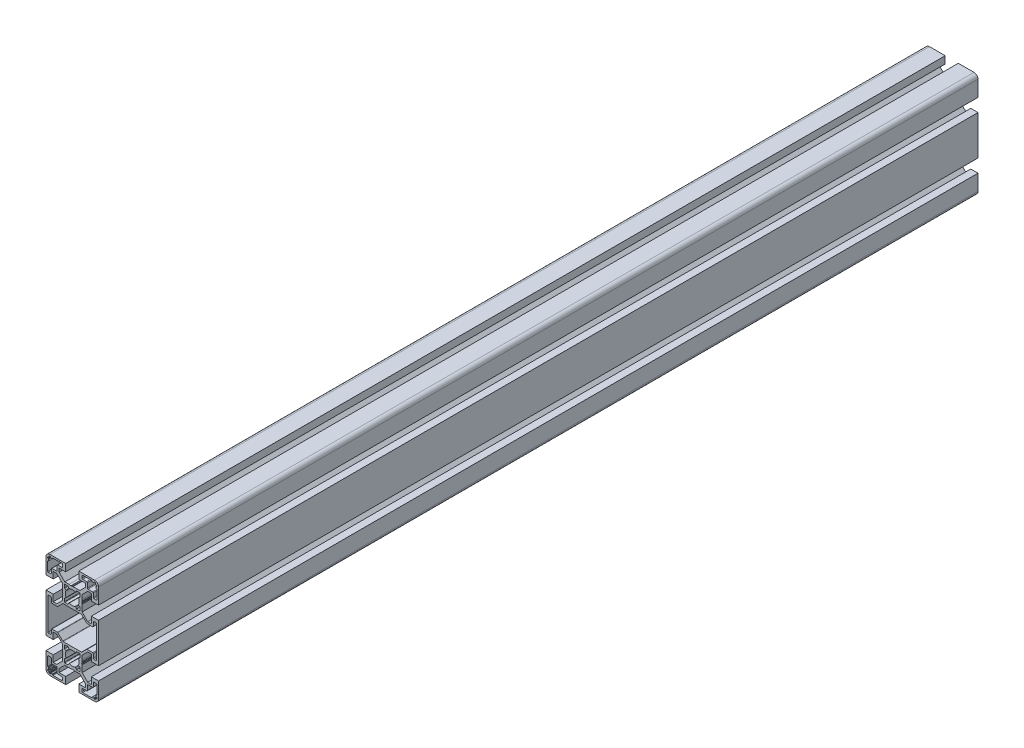
SolidWorks part; units mm, degrees
ref_plane "Front Plane" through (0, 0, 0) normal (0, 0, 1) x (1, 0, 0)
ref_plane "Top Plane" through (0, 0, 0) normal (0, 1, 0) x (1, 0, 0)
ref_plane "Right Plane" through (0, 0, 0) normal (1, 0, 0) x (0, 0, -1)
sketch "Sketch1" plane through (0, 0, 0) normal (0, 0, 1) x (1, 0, 0)
  line L0 (-14.5, -30) -> (-14.5, -25)
  line L1 (-14.5, -25) -> (-20, -25)
  line L2 (-20, -25) -> (-20, -37)
  line L3 (-17, -40) -> (-5, -40)
  line L4 (-5, -40) -> (-5, -34.5)
  line L5 (-5, -34.5) -> (-10, -34.5)
  line L6 (-10, -34.5) -> (-10, -31.7678)
  line L7 (-10, -31.7678) -> (-5.7322, -27.5)
  line L8 (-5.7322, -27.5) -> (-0.6536, -27.5)
  line L9 (-0.4036, -27.433) -> (0, -27.2)
  line L10 (0, -27.2) -> (0.2696, -27.3557)
  line L11 (0.7696, -27.3557) -> (1.0184, -27.212)
  line L12 (1.0184, -27.212) -> (2.5, -27.5)
  line L13 (2.5, -27.5) -> (5.7322, -27.5)
  line L14 (5.7322, -27.5) -> (10, -31.7678)
  line L15 (10, -31.7678) -> (10, -34.5)
  line L16 (10, -34.5) -> (5, -34.5)
  line L17 (5, -34.5) -> (5, -40)
  line L18 (5, -40) -> (17, -40)
  line L19 (20, -37) -> (20, -25)
  line L20 (20, -25) -> (14.5, -25)
  line L21 (14.5, -25) -> (14.5, -30)
  line L22 (14.5, -30) -> (11.7678, -30)
  line L23 (11.7678, -30) -> (7.5, -25.7322)
  line L24 (7.5, -25.7322) -> (7.5, -20.6536)
  line L25 (7.433, -20.4036) -> (7.2, -20)
  line L26 (7.2, -20) -> (7.3557, -19.7304)
  line L27 (7.3557, -19.2304) -> (7.212, -18.9816)
  line L28 (7.212, -18.9816) -> (7.5, -17.5)
  line L29 (7.5, -17.5) -> (7.5, -14.2678)
  line L30 (7.5, -14.2678) -> (11.7678, -10)
  line L31 (11.7678, -10) -> (14.5, -10)
  line L32 (14.5, -10) -> (14.5, -15)
  line L33 (14.5, -15) -> (20, -15)
  line L34 (20, -15) -> (20, 15)
  line L35 (20, 15) -> (14.5, 15)
  line L36 (14.5, 15) -> (14.5, 10)
  line L37 (14.5, 10) -> (11.7678, 10)
  line L38 (11.7678, 10) -> (7.5, 14.2678)
  line L39 (7.5, 14.2678) -> (7.5, 19.3464)
  line L40 (7.433, 19.5964) -> (7.2, 20)
  line L41 (7.2, 20) -> (7.3557, 20.2696)
  line L42 (7.3557, 20.7696) -> (7.212, 21.0184)
  line L43 (7.212, 21.0184) -> (7.5, 22.5)
  line L44 (7.5, 22.5) -> (7.5, 25.7322)
  line L45 (7.5, 25.7322) -> (11.7678, 30)
  line L46 (11.7678, 30) -> (14.5, 30)
  line L47 (14.5, 30) -> (14.5, 25)
  line L48 (14.5, 25) -> (20, 25)
  line L49 (20, 25) -> (20, 37)
  line L50 (17, 40) -> (5, 40)
  line L51 (5, 40) -> (5, 34.5)
  line L52 (5, 34.5) -> (10, 34.5)
  line L53 (10, 34.5) -> (10, 31.7678)
  line L54 (10, 31.7678) -> (5.7322, 27.5)
  line L55 (5.7322, 27.5) -> (0.6536, 27.5)
  line L56 (0.4036, 27.433) -> (0, 27.2)
  line L57 (0, 27.2) -> (-0.2696, 27.3557)
  line L58 (-0.7696, 27.3557) -> (-1.0184, 27.212)
  line L59 (-1.0184, 27.212) -> (-2.5, 27.5)
  line L60 (-2.5, 27.5) -> (-5.7322, 27.5)
  line L61 (-5.7322, 27.5) -> (-10, 31.7678)
  line L62 (-10, 31.7678) -> (-10, 34.5)
  line L63 (-10, 34.5) -> (-5, 34.5)
  line L64 (-5, 34.5) -> (-5, 40)
  line L65 (-5, 40) -> (-17, 40)
  line L66 (-20, 37) -> (-20, 25)
  line L67 (-20, 25) -> (-14.5, 25)
  line L68 (-14.5, 25) -> (-14.5, 30)
  line L69 (-14.5, 30) -> (-11.7678, 30)
  line L70 (-11.7678, 30) -> (-7.5, 25.7322)
  line L71 (-7.5, 25.7322) -> (-7.5, 20.6536)
  line L72 (-7.433, 20.4036) -> (-7.2, 20)
  line L73 (-7.2, 20) -> (-7.3557, 19.7304)
  line L74 (-7.3557, 19.2304) -> (-7.212, 18.9816)
  line L75 (-7.212, 18.9816) -> (-7.5, 17.5)
  line L76 (-7.5, 17.5) -> (-7.5, 14.2678)
  line L77 (-7.5, 14.2678) -> (-11.7678, 10)
  line L78 (-11.7678, 10) -> (-14.5, 10)
  line L79 (-14.5, 10) -> (-14.5, 15)
  line L80 (-14.5, 15) -> (-20, 15)
  line L81 (-20, 15) -> (-20, -15)
  line L82 (-20, -15) -> (-14.5, -15)
  line L83 (-14.5, -15) -> (-14.5, -10)
  line L84 (-14.5, -10) -> (-11.7678, -10)
  line L85 (-11.7678, -10) -> (-7.5, -14.2678)
  line L86 (-7.5, -14.2678) -> (-7.5, -19.3464)
  line L87 (-7.433, -19.5964) -> (-7.2, -20)
  line L88 (-7.2, -20) -> (-7.3557, -20.2696)
  line L89 (-7.3557, -20.7696) -> (-7.212, -21.0184)
  line L90 (-7.212, -21.0184) -> (-7.5, -22.5)
  line L91 (-7.5, -22.5) -> (-7.5, -25.7322)
  line L92 (-7.5, -25.7322) -> (-11.7678, -30)
  line L93 (-11.7678, -30) -> (-14.5, -30)
  line L94 (7.5, -38.2) -> (7.5, -36.5)
  line L95 (8, -36) -> (11, -36)
  line L96 (11.5, -35.5) -> (11.5, -32)
  line L97 (12, -31.5) -> (15.5, -31.5)
  line L98 (16, -31) -> (16, -28)
  line L99 (16.5, -27.5) -> (18.2, -27.5)
  line L100 (18.7, -28) -> (18.7, -34.7)
  line L101 (18.4, -35) -> (18.3, -35)
  line L102 (18, -35.3) -> (18, -36.3)
  line L103 (18.3, -36.6) -> (18.4, -36.6)
  line L104 (18.7, -36.9) -> (18.7, -37.3)
  line L105 (18.4, -37.6) -> (17.9, -37.6)
  line L106 (17.6, -37.9) -> (17.6, -38.4)
  line L107 (17.3, -38.7) -> (16.9, -38.7)
  line L108 (16.6, -38.4) -> (16.6, -38.3)
  line L109 (16.3, -38) -> (15.3, -38)
  line L110 (15, -38.3) -> (15, -38.4)
  line L111 (14.7, -38.7) -> (8, -38.7)
  line L112 (7.5, 36.5) -> (7.5, 38.2)
  line L113 (8, 38.7) -> (14.7, 38.7)
  line L114 (15, 38.4) -> (15, 38.3)
  line L115 (15.3, 38) -> (16.3, 38)
  line L116 (16.6, 38.3) -> (16.6, 38.4)
  line L117 (16.9, 38.7) -> (17.3, 38.7)
  line L118 (17.6, 38.4) -> (17.6, 37.9)
  line L119 (17.9, 37.6) -> (18.4, 37.6)
  line L120 (18.7, 37.3) -> (18.7, 36.9)
  line L121 (18.4, 36.6) -> (18.3, 36.6)
  line L122 (18, 36.3) -> (18, 35.3)
  line L123 (18.3, 35) -> (18.4, 35)
  line L124 (18.7, 34.7) -> (18.7, 28)
  line L125 (18.2, 27.5) -> (16.5, 27.5)
  line L126 (16, 28) -> (16, 31)
  line L127 (15.5, 31.5) -> (12, 31.5)
  line L128 (11.5, 32) -> (11.5, 35.5)
  line L129 (11, 36) -> (8, 36)
  line L130 (-18.5, -12) -> (-18.5, 12)
  line L131 (-18, 12.5) -> (-16.5, 12.5)
  line L132 (-16, 12) -> (-16, 9)
  line L133 (-15.5, 8.5) -> (-11.3536, 8.5)
  line L134 (-11, 8.6464) -> (-7.2929, 12.3536)
  line L135 (-6.9393, 12.5) -> (6.9393, 12.5)
  line L136 (7.2929, 12.3536) -> (11, 8.6464)
  line L137 (11.3536, 8.5) -> (15.5, 8.5)
  line L138 (16, 9) -> (16, 12)
  line L139 (16.5, 12.5) -> (18, 12.5)
  line L140 (18.5, 12) -> (18.5, -12)
  line L141 (18, -12.5) -> (16.5, -12.5)
  line L142 (16, -12) -> (16, -9)
  line L143 (15.5, -8.5) -> (11.3536, -8.5)
  line L144 (11, -8.6464) -> (7.2929, -12.3536)
  line L145 (6.9393, -12.5) -> (-6.9393, -12.5)
  line L146 (-7.2929, -12.3536) -> (-11, -8.6464)
  line L147 (-11.3536, -8.5) -> (-15.5, -8.5)
  line L148 (-16, -9) -> (-16, -12)
  line L149 (-16.5, -12.5) -> (-18, -12.5)
  line L150 (-18.7, 36.9) -> (-18.7, 37.3)
  line L151 (-18.4, 37.6) -> (-17.9, 37.6)
  line L152 (-17.6, 37.9) -> (-17.6, 38.4)
  line L153 (-17.3, 38.7) -> (-16.9, 38.7)
  line L154 (-16.6, 38.4) -> (-16.6, 38.3)
  line L155 (-16.3, 38) -> (-15.3, 38)
  line L156 (-15, 38.3) -> (-15, 38.4)
  line L157 (-14.7, 38.7) -> (-8, 38.7)
  line L158 (-7.5, 38.2) -> (-7.5, 36.5)
  line L159 (-8, 36) -> (-11, 36)
  line L160 (-11.5, 35.5) -> (-11.5, 32)
  line L161 (-12, 31.5) -> (-15.5, 31.5)
  line L162 (-16, 31) -> (-16, 28)
  line L163 (-16.5, 27.5) -> (-18.2, 27.5)
  line L164 (-18.7, 28) -> (-18.7, 34.7)
  line L165 (-18.4, 35) -> (-18.3, 35)
  line L166 (-18, 35.3) -> (-18, 36.3)
  line L167 (-18.3, 36.6) -> (-18.4, 36.6)
  line L168 (-17.9, -37.6) -> (-18.4, -37.6)
  line L169 (-18.7, -37.3) -> (-18.7, -36.9)
  line L170 (-18.4, -36.6) -> (-18.3, -36.6)
  line L171 (-18, -36.3) -> (-18, -35.3)
  line L172 (-18.3, -35) -> (-18.4, -35)
  line L173 (-18.7, -34.7) -> (-18.7, -28)
  line L174 (-18.2, -27.5) -> (-16.5, -27.5)
  line L175 (-16, -28) -> (-16, -31)
  line L176 (-15.5, -31.5) -> (-12, -31.5)
  line L177 (-11.5, -32) -> (-11.5, -35.5)
  line L178 (-11, -36) -> (-8, -36)
  line L179 (-7.5, -36.5) -> (-7.5, -38.2)
  line L180 (-8, -38.7) -> (-14.7, -38.7)
  line L181 (-15, -38.4) -> (-15, -38.3)
  line L182 (-15.3, -38) -> (-16.3, -38)
  line L183 (-16.6, -38.3) -> (-16.6, -38.4)
  line L184 (-16.9, -38.7) -> (-17.3, -38.7)
  line L185 (-17.6, -38.4) -> (-17.6, -37.9)
  line L186 (-6, 14.3) -> (-6, 16.62)
  line L187 (-5.8412, 16.8847) -> (-4.8899, 17.3921)
  line L188 (-4.8899, 22.6079) -> (-5.8412, 23.1153)
  line L189 (-6, 23.38) -> (-6, 25.7)
  line L190 (-5.7, 26) -> (-3.38, 26)
  line L191 (-3.1153, 25.8412) -> (-2.6079, 24.8899)
  line L192 (2.6079, 24.8899) -> (3.1153, 25.8412)
  line L193 (3.38, 26) -> (5.7, 26)
  line L194 (6, 25.7) -> (6, 23.38)
  line L195 (5.8412, 23.1153) -> (4.8899, 22.6079)
  line L196 (4.8899, 17.3921) -> (5.8412, 16.8847)
  line L197 (6, 16.62) -> (6, 14.3)
  line L198 (5.7, 14) -> (3.38, 14)
  line L199 (3.1153, 14.1588) -> (2.6079, 15.1101)
  line L200 (-2.6079, 15.1101) -> (-3.1153, 14.1588)
  line L201 (-3.38, 14) -> (-5.7, 14)
  line L202 (-6, -25.7) -> (-6, -23.38)
  line L203 (-5.8412, -23.1153) -> (-4.8899, -22.6079)
  line L204 (-4.8899, -17.3921) -> (-5.8412, -16.8847)
  line L205 (-6, -16.62) -> (-6, -14.3)
  line L206 (-5.7, -14) -> (-3.38, -14)
  line L207 (-3.1153, -14.1588) -> (-2.6079, -15.1101)
  line L208 (2.6079, -15.1101) -> (3.1153, -14.1588)
  line L209 (3.38, -14) -> (5.7, -14)
  line L210 (6, -14.3) -> (6, -16.62)
  line L211 (5.8412, -16.8847) -> (4.8899, -17.3921)
  line L212 (4.8899, -22.6079) -> (5.8412, -23.1153)
  line L213 (6, -23.38) -> (6, -25.7)
  line L214 (5.7, -26) -> (3.38, -26)
  line L215 (3.1153, -25.8412) -> (2.6079, -24.8899)
  line L216 (-2.6079, -24.8899) -> (-3.1153, -25.8412)
  line L217 (-3.38, -26) -> (-5.7, -26)
  arc A0 (-20, -37) -> (-17, -40) centre (-17, -37) ccw
  arc A1 (-0.6536, -27.5) -> (-0.4036, -27.433) centre (-0.6536, -27) ccw
  arc A2 (0.2696, -27.3557) -> (0.7696, -27.3557) centre (0.5196, -26.9226) ccw
  arc A3 (17, -40) -> (20, -37) centre (17, -37) ccw
  arc A4 (7.5, -20.6536) -> (7.433, -20.4036) centre (7, -20.6536) ccw
  arc A5 (7.3557, -19.7304) -> (7.3557, -19.2304) centre (6.9226, -19.4804) ccw
  arc A6 (7.5, 19.3464) -> (7.433, 19.5964) centre (7, 19.3464) ccw
  arc A7 (7.3557, 20.2696) -> (7.3557, 20.7696) centre (6.9226, 20.5196) ccw
  arc A8 (20, 37) -> (17, 40) centre (17, 37) ccw
  arc A9 (0.6536, 27.5) -> (0.4036, 27.433) centre (0.6536, 27) ccw
  arc A10 (-0.2696, 27.3557) -> (-0.7696, 27.3557) centre (-0.5196, 26.9226) ccw
  arc A11 (-17, 40) -> (-20, 37) centre (-17, 37) ccw
  arc A12 (-7.5, 20.6536) -> (-7.433, 20.4036) centre (-7, 20.6536) ccw
  arc A13 (-7.3557, 19.7304) -> (-7.3557, 19.2304) centre (-6.9226, 19.4804) ccw
  arc A14 (-7.5, -19.3464) -> (-7.433, -19.5964) centre (-7, -19.3464) ccw
  arc A15 (-7.3557, -20.2696) -> (-7.3557, -20.7696) centre (-6.9226, -20.5196) ccw
  arc A16 (8, -38.7) -> (7.5, -38.2) centre (8, -38.2) cw
  arc A17 (7.5, -36.5) -> (8, -36) centre (8, -36.5) cw
  arc A18 (11, -36) -> (11.5, -35.5) centre (11, -35.5) ccw
  arc A19 (11.5, -32) -> (12, -31.5) centre (12, -32) cw
  arc A20 (15.5, -31.5) -> (16, -31) centre (15.5, -31) ccw
  arc A21 (16, -28) -> (16.5, -27.5) centre (16.5, -28) cw
  arc A22 (18.2, -27.5) -> (18.7, -28) centre (18.2, -28) cw
  arc A23 (18.7, -34.7) -> (18.4, -35) centre (18.4, -34.7) cw
  arc A24 (18.3, -35) -> (18, -35.3) centre (18.3, -35.3) ccw
  arc A25 (18, -36.3) -> (18.3, -36.6) centre (18.3, -36.3) ccw
  arc A26 (18.4, -36.6) -> (18.7, -36.9) centre (18.4, -36.9) cw
  arc A27 (18.7, -37.3) -> (18.4, -37.6) centre (18.4, -37.3) cw
  arc A28 (17.9, -37.6) -> (17.6, -37.9) centre (17.9, -37.9) ccw
  arc A29 (17.6, -38.4) -> (17.3, -38.7) centre (17.3, -38.4) cw
  arc A30 (16.9, -38.7) -> (16.6, -38.4) centre (16.9, -38.4) cw
  arc A31 (16.6, -38.3) -> (16.3, -38) centre (16.3, -38.3) ccw
  arc A32 (15.3, -38) -> (15, -38.3) centre (15.3, -38.3) ccw
  arc A33 (15, -38.4) -> (14.7, -38.7) centre (14.7, -38.4) cw
  arc A34 (8, 36) -> (7.5, 36.5) centre (8, 36.5) cw
  arc A35 (7.5, 38.2) -> (8, 38.7) centre (8, 38.2) cw
  arc A36 (14.7, 38.7) -> (15, 38.4) centre (14.7, 38.4) cw
  arc A37 (15, 38.3) -> (15.3, 38) centre (15.3, 38.3) ccw
  arc A38 (16.3, 38) -> (16.6, 38.3) centre (16.3, 38.3) ccw
  arc A39 (16.6, 38.4) -> (16.9, 38.7) centre (16.9, 38.4) cw
  arc A40 (17.3, 38.7) -> (17.6, 38.4) centre (17.3, 38.4) cw
  arc A41 (17.6, 37.9) -> (17.9, 37.6) centre (17.9, 37.9) ccw
  arc A42 (18.4, 37.6) -> (18.7, 37.3) centre (18.4, 37.3) cw
  arc A43 (18.7, 36.9) -> (18.4, 36.6) centre (18.4, 36.9) cw
  arc A44 (18.3, 36.6) -> (18, 36.3) centre (18.3, 36.3) ccw
  arc A45 (18, 35.3) -> (18.3, 35) centre (18.3, 35.3) ccw
  arc A46 (18.4, 35) -> (18.7, 34.7) centre (18.4, 34.7) cw
  arc A47 (18.7, 28) -> (18.2, 27.5) centre (18.2, 28) cw
  arc A48 (16.5, 27.5) -> (16, 28) centre (16.5, 28) cw
  arc A49 (16, 31) -> (15.5, 31.5) centre (15.5, 31) ccw
  arc A50 (12, 31.5) -> (11.5, 32) centre (12, 32) cw
  arc A51 (11.5, 35.5) -> (11, 36) centre (11, 35.5) ccw
  arc A52 (-18, -12.5) -> (-18.5, -12) centre (-18, -12) cw
  arc A53 (-18.5, 12) -> (-18, 12.5) centre (-18, 12) cw
  arc A54 (-16.5, 12.5) -> (-16, 12) centre (-16.5, 12) cw
  arc A55 (-16, 9) -> (-15.5, 8.5) centre (-15.5, 9) ccw
  arc A56 (-11.3536, 8.5) -> (-11, 8.6464) centre (-11.3536, 9) ccw
  arc A57 (-7.2929, 12.3536) -> (-6.9393, 12.5) centre (-6.9393, 12) cw
  arc A58 (6.9393, 12.5) -> (7.2929, 12.3536) centre (6.9393, 12) cw
  arc A59 (11, 8.6464) -> (11.3536, 8.5) centre (11.3536, 9) ccw
  arc A60 (15.5, 8.5) -> (16, 9) centre (15.5, 9) ccw
  arc A61 (16, 12) -> (16.5, 12.5) centre (16.5, 12) cw
  arc A62 (18, 12.5) -> (18.5, 12) centre (18, 12) cw
  arc A63 (18.5, -12) -> (18, -12.5) centre (18, -12) cw
  arc A64 (16.5, -12.5) -> (16, -12) centre (16.5, -12) cw
  arc A65 (16, -9) -> (15.5, -8.5) centre (15.5, -9) ccw
  arc A66 (11.3536, -8.5) -> (11, -8.6464) centre (11.3536, -9) ccw
  arc A67 (7.2929, -12.3536) -> (6.9393, -12.5) centre (6.9393, -12) cw
  arc A68 (-6.9393, -12.5) -> (-7.2929, -12.3536) centre (-6.9393, -12) cw
  arc A69 (-11, -8.6464) -> (-11.3536, -8.5) centre (-11.3536, -9) ccw
  arc A70 (-15.5, -8.5) -> (-16, -9) centre (-15.5, -9) ccw
  arc A71 (-16, -12) -> (-16.5, -12.5) centre (-16.5, -12) cw
  arc A72 (-18.4, 36.6) -> (-18.7, 36.9) centre (-18.4, 36.9) cw
  arc A73 (-18.7, 37.3) -> (-18.4, 37.6) centre (-18.4, 37.3) cw
  arc A74 (-17.9, 37.6) -> (-17.6, 37.9) centre (-17.9, 37.9) ccw
  arc A75 (-17.6, 38.4) -> (-17.3, 38.7) centre (-17.3, 38.4) cw
  arc A76 (-16.9, 38.7) -> (-16.6, 38.4) centre (-16.9, 38.4) cw
  arc A77 (-16.6, 38.3) -> (-16.3, 38) centre (-16.3, 38.3) ccw
  arc A78 (-15.3, 38) -> (-15, 38.3) centre (-15.3, 38.3) ccw
  arc A79 (-15, 38.4) -> (-14.7, 38.7) centre (-14.7, 38.4) cw
  arc A80 (-8, 38.7) -> (-7.5, 38.2) centre (-8, 38.2) cw
  arc A81 (-7.5, 36.5) -> (-8, 36) centre (-8, 36.5) cw
  arc A82 (-11, 36) -> (-11.5, 35.5) centre (-11, 35.5) ccw
  arc A83 (-11.5, 32) -> (-12, 31.5) centre (-12, 32) cw
  arc A84 (-15.5, 31.5) -> (-16, 31) centre (-15.5, 31) ccw
  arc A85 (-16, 28) -> (-16.5, 27.5) centre (-16.5, 28) cw
  arc A86 (-18.2, 27.5) -> (-18.7, 28) centre (-18.2, 28) cw
  arc A87 (-18.7, 34.7) -> (-18.4, 35) centre (-18.4, 34.7) cw
  arc A88 (-18.3, 35) -> (-18, 35.3) centre (-18.3, 35.3) ccw
  arc A89 (-18, 36.3) -> (-18.3, 36.6) centre (-18.3, 36.3) ccw
  arc A90 (-18.4, -37.6) -> (-18.7, -37.3) centre (-18.4, -37.3) cw
  arc A91 (-18.7, -36.9) -> (-18.4, -36.6) centre (-18.4, -36.9) cw
  arc A92 (-18.3, -36.6) -> (-18, -36.3) centre (-18.3, -36.3) ccw
  arc A93 (-18, -35.3) -> (-18.3, -35) centre (-18.3, -35.3) ccw
  arc A94 (-18.4, -35) -> (-18.7, -34.7) centre (-18.4, -34.7) cw
  arc A95 (-18.7, -28) -> (-18.2, -27.5) centre (-18.2, -28) cw
  arc A96 (-16.5, -27.5) -> (-16, -28) centre (-16.5, -28) cw
  arc A97 (-16, -31) -> (-15.5, -31.5) centre (-15.5, -31) ccw
  arc A98 (-12, -31.5) -> (-11.5, -32) centre (-12, -32) cw
  arc A99 (-11.5, -35.5) -> (-11, -36) centre (-11, -35.5) ccw
  arc A100 (-8, -36) -> (-7.5, -36.5) centre (-8, -36.5) cw
  arc A101 (-7.5, -38.2) -> (-8, -38.7) centre (-8, -38.2) cw
  arc A102 (-14.7, -38.7) -> (-15, -38.4) centre (-14.7, -38.4) cw
  arc A103 (-15, -38.3) -> (-15.3, -38) centre (-15.3, -38.3) ccw
  arc A104 (-16.3, -38) -> (-16.6, -38.3) centre (-16.3, -38.3) ccw
  arc A105 (-16.6, -38.4) -> (-16.9, -38.7) centre (-16.9, -38.4) cw
  arc A106 (-17.3, -38.7) -> (-17.6, -38.4) centre (-17.3, -38.4) cw
  arc A107 (-17.6, -37.9) -> (-17.9, -37.6) centre (-17.9, -37.9) ccw
  arc A108 (-5.7, 14) -> (-6, 14.3) centre (-5.7, 14.3) cw
  arc A109 (-6, 16.62) -> (-5.8412, 16.8847) centre (-5.7, 16.62) cw
  arc A110 (-4.8899, 17.3921) -> (-4.7591, 17.7834) centre (-5.0311, 17.6568) ccw
  arc A111 (-4.7591, 17.7834) -> (-4.7591, 22.2166) centre (0, 20) cw
  arc A112 (-4.7591, 22.2166) -> (-4.8899, 22.6079) centre (-5.0311, 22.3432) ccw
  arc A113 (-5.8412, 23.1153) -> (-6, 23.38) centre (-5.7, 23.38) cw
  arc A114 (-6, 25.7) -> (-5.7, 26) centre (-5.7, 25.7) cw
  arc A115 (-3.38, 26) -> (-3.1153, 25.8412) centre (-3.38, 25.7) cw
  arc A116 (-2.6079, 24.8899) -> (-2.2166, 24.7591) centre (-2.3432, 25.0311) ccw
  arc A117 (-2.2166, 24.7591) -> (2.2166, 24.7591) centre (0, 20) cw
  arc A118 (2.2166, 24.7591) -> (2.6079, 24.8899) centre (2.3432, 25.0311) ccw
  arc A119 (3.1153, 25.8412) -> (3.38, 26) centre (3.38, 25.7) cw
  arc A120 (5.7, 26) -> (6, 25.7) centre (5.7, 25.7) cw
  arc A121 (6, 23.38) -> (5.8412, 23.1153) centre (5.7, 23.38) cw
  arc A122 (4.8899, 22.6079) -> (4.7591, 22.2166) centre (5.0311, 22.3432) ccw
  arc A123 (4.7591, 22.2166) -> (4.7591, 17.7834) centre (0, 20) cw
  arc A124 (4.7591, 17.7834) -> (4.8899, 17.3921) centre (5.0311, 17.6568) ccw
  arc A125 (5.8412, 16.8847) -> (6, 16.62) centre (5.7, 16.62) cw
  arc A126 (6, 14.3) -> (5.7, 14) centre (5.7, 14.3) cw
  arc A127 (3.38, 14) -> (3.1153, 14.1588) centre (3.38, 14.3) cw
  arc A128 (2.6079, 15.1101) -> (2.2166, 15.2409) centre (2.3432, 14.9689) ccw
  arc A129 (2.2166, 15.2409) -> (-2.2166, 15.2409) centre (0, 20) cw
  arc A130 (-2.2166, 15.2409) -> (-2.6079, 15.1101) centre (-2.3432, 14.9689) ccw
  arc A131 (-3.1153, 14.1588) -> (-3.38, 14) centre (-3.38, 14.3) cw
  arc A132 (-5.7, -26) -> (-6, -25.7) centre (-5.7, -25.7) cw
  arc A133 (-6, -23.38) -> (-5.8412, -23.1153) centre (-5.7, -23.38) cw
  arc A134 (-4.8899, -22.6079) -> (-4.7591, -22.2166) centre (-5.0311, -22.3432) ccw
  arc A135 (-4.7591, -22.2166) -> (-4.7591, -17.7834) centre (0, -20) cw
  arc A136 (-4.7591, -17.7834) -> (-4.8899, -17.3921) centre (-5.0311, -17.6568) ccw
  arc A137 (-5.8412, -16.8847) -> (-6, -16.62) centre (-5.7, -16.62) cw
  arc A138 (-6, -14.3) -> (-5.7, -14) centre (-5.7, -14.3) cw
  arc A139 (-3.38, -14) -> (-3.1153, -14.1588) centre (-3.38, -14.3) cw
  arc A140 (-2.6079, -15.1101) -> (-2.2166, -15.2409) centre (-2.3432, -14.9689) ccw
  arc A141 (-2.2166, -15.2409) -> (2.2166, -15.2409) centre (0, -20) cw
  arc A142 (2.2166, -15.2409) -> (2.6079, -15.1101) centre (2.3432, -14.9689) ccw
  arc A143 (3.1153, -14.1588) -> (3.38, -14) centre (3.38, -14.3) cw
  arc A144 (5.7, -14) -> (6, -14.3) centre (5.7, -14.3) cw
  arc A145 (6, -16.62) -> (5.8412, -16.8847) centre (5.7, -16.62) cw
  arc A146 (4.8899, -17.3921) -> (4.7591, -17.7834) centre (5.0311, -17.6568) ccw
  arc A147 (4.7591, -17.7834) -> (4.7591, -22.2166) centre (0, -20) cw
  arc A148 (4.7591, -22.2166) -> (4.8899, -22.6079) centre (5.0311, -22.3432) ccw
  arc A149 (5.8412, -23.1153) -> (6, -23.38) centre (5.7, -23.38) cw
  arc A150 (6, -25.7) -> (5.7, -26) centre (5.7, -25.7) cw
  arc A151 (3.38, -26) -> (3.1153, -25.8412) centre (3.38, -25.7) cw
  arc A152 (2.6079, -24.8899) -> (2.2166, -24.7591) centre (2.3432, -25.0311) ccw
  arc A153 (2.2166, -24.7591) -> (-2.2166, -24.7591) centre (0, -20) cw
  arc A154 (-2.2166, -24.7591) -> (-2.6079, -24.8899) centre (-2.3432, -25.0311) ccw
  arc A155 (-3.1153, -25.8412) -> (-3.38, -26) centre (-3.38, -25.7) cw
extrude "Boss-Extrude1" add sketch "Sketch1" against normal blind 670
